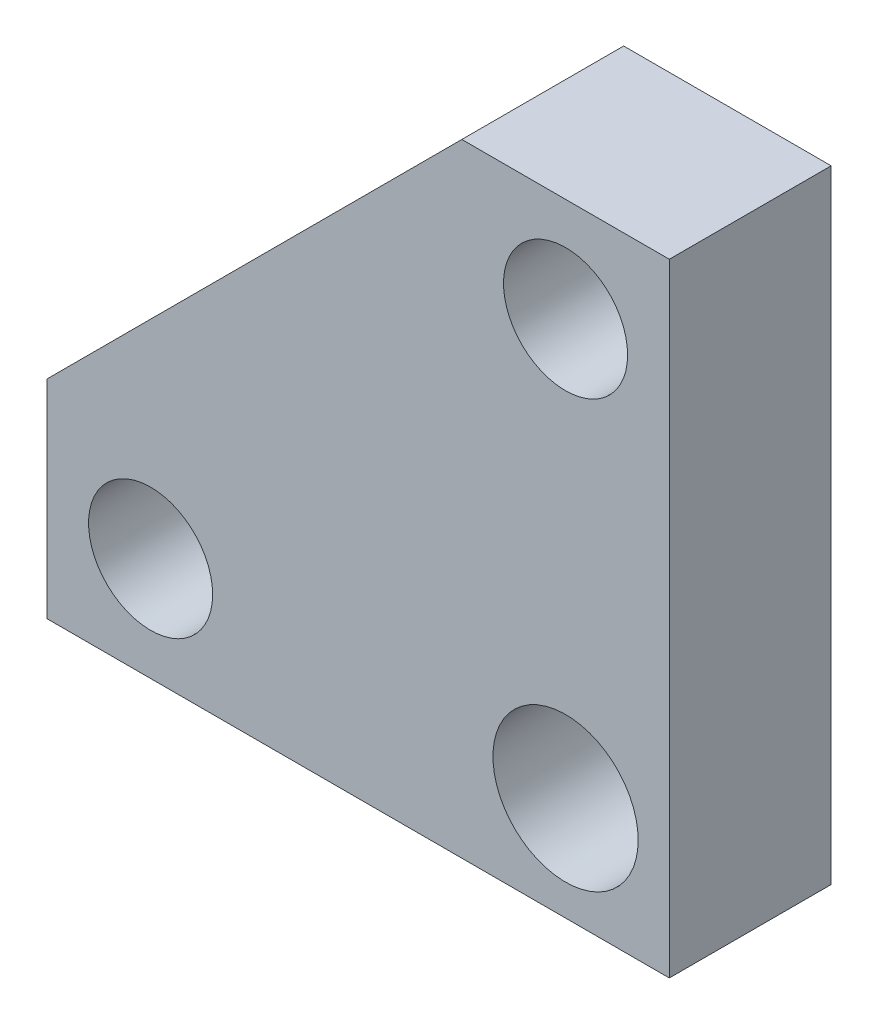
SolidWorks part; units mm, degrees
ref_plane "Plan de face" through (0, 0, 0) normal (0, 0, 1) x (1, 0, 0)
ref_plane "Plan de dessus" through (0, 0, 0) normal (0, 1, 0) x (1, 0, 0)
ref_plane "Plan de droite" through (0, 0, 0) normal (1, 0, 0) x (0, 0, -1)
sketch "Esquisse1" plane through (0, 0, 0) normal (0, 0, 1) x (1, 0, 0)
  line L0 (0, 0) -> (0, 30)
  line L1 (0, 30) -> (-10, 30)
  line L2 (-10, 30) -> (-30, 10)
  line L3 (-30, 10) -> (-30, 0)
  line L4 (-30, 0) -> (0, 0)
  line L5 (-5, 25) -> (-5, 5) construction
  line L6 (-5, 5) -> (-25, 5) construction
  circle A0 centre (-5, 25) radius 2.99
  circle A1 centre (-25, 5) radius 2.99
  circle A2 centre (-5, 5) radius 3.5
  dimension "D9" = 5.98
  dimension "D10" = 5.98
  dimension "D11" = 7
  dimension "D1" = 10
  dimension "D2" = 10
  dimension "D3" = 30
  dimension "D4" = 30
  dimension "D5" = 5
  dimension "D6" = 5
  dimension "D7" = 20
  dimension "D8" = 20
extrude "Extrusion1" add sketch "Esquisse1" along normal mid plane 7.8
